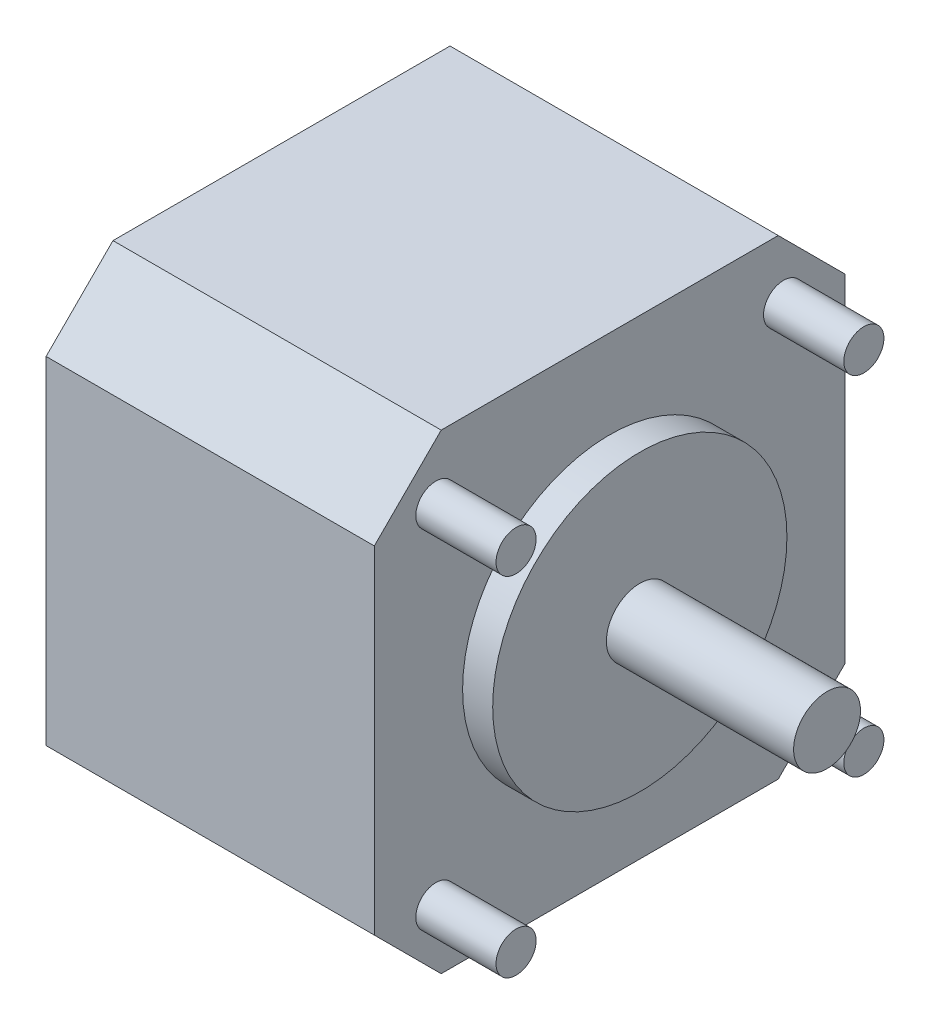
SolidWorks part; units mm, degrees
ref_plane "Front" through (0, 0, 0) normal (0, 0, 1) x (1, 0, 0)
ref_plane "Top" through (0, 0, 0) normal (0, 1, 0) x (1, 0, 0)
ref_plane "Right" through (0, 0, 0) normal (1, 0, 0) x (0, 0, -1)
sketch "Sketch1" plane through (0, 0, 0) normal (0, 1, 0) x (1, 0, 0)
  line L1 (0, 0) -> (24.54, 0)
  line L2 (0, 0) -> (0, 35.2)
  line L3 (0, 35.2) -> (24.54, 35.2)
  line L4 (24.54, 0) -> (24.54, 35.2)
  dimension "D1" = 35.2
  dimension "D2" = 24.54
extrude "Main body" add sketch "Sketch1" along normal blind 35.2
sketch "Sketch2" plane through (24.54, 0, 0) normal (1, 0, 0) x (0, 0, -1)
  line L0 (0, 17.6) -> (35.2, 17.6) construction
  line L1 (0, 35.2) -> (0, 0) construction
  line L2 (35.2, 35.2) -> (35.2, 0) construction
  circle A0 centre (17.6, 17.6) radius 11
  dimension "D1" = 22
extrude "lip" add sketch "Sketch2" along normal blind 2.25
sketch "Sketch3" plane through (26.79, 0, 0) normal (1, 0, 0) x (0, 0, -1)
  line L0 (35.2, 17.6) -> (0, 17.6) construction
  line L1 (35.2, 35.2) -> (35.2, 0) construction
  line L2 (0, 35.2) -> (0, 0) construction
  circle A0 centre (17.6, 17.6) radius 2.5
  dimension "D1" = 5
extrude "shaft" add sketch "Sketch3" along normal blind 14
chamfer "Chamfer1" distance 5 angle 45 4 edges at (12.27, 35.2, 0) (12.27, 0, 0) (12.27, 0, -35.2) (12.27, 35.2, -35.2)
sketch "Sketch4" plane through (24.54, 0, 0) normal (1, 0, 0) x (0, 0, -1)
  line L0 (0, 17.6) -> (35.2, 17.6) construction
  line L1 (0, 30.2) -> (0, 5) construction
  line L2 (35.2, 30.2) -> (35.2, 5) construction
  line L3 (17.6, 35.2) -> (17.6, 0) construction
  line L4 (5, 35.2) -> (30.2, 35.2) construction
  line L5 (5, 0) -> (30.2, 0) construction
  circle A0 centre (30.6, 30.6) radius 1.5
  circle A1 centre (30.6, 4.6) radius 1.5
  circle A2 centre (4.6, 30.6) radius 1.5
  circle A3 centre (4.6, 4.6) radius 1.5
  dimension "D1" = 3
  dimension "D2" = 26
  dimension "D3" = 13
  dimension "D4" = 13
  dimension "D5" = 2
extrude "Boss-Extrude4" add sketch "Sketch4" along normal blind 6
